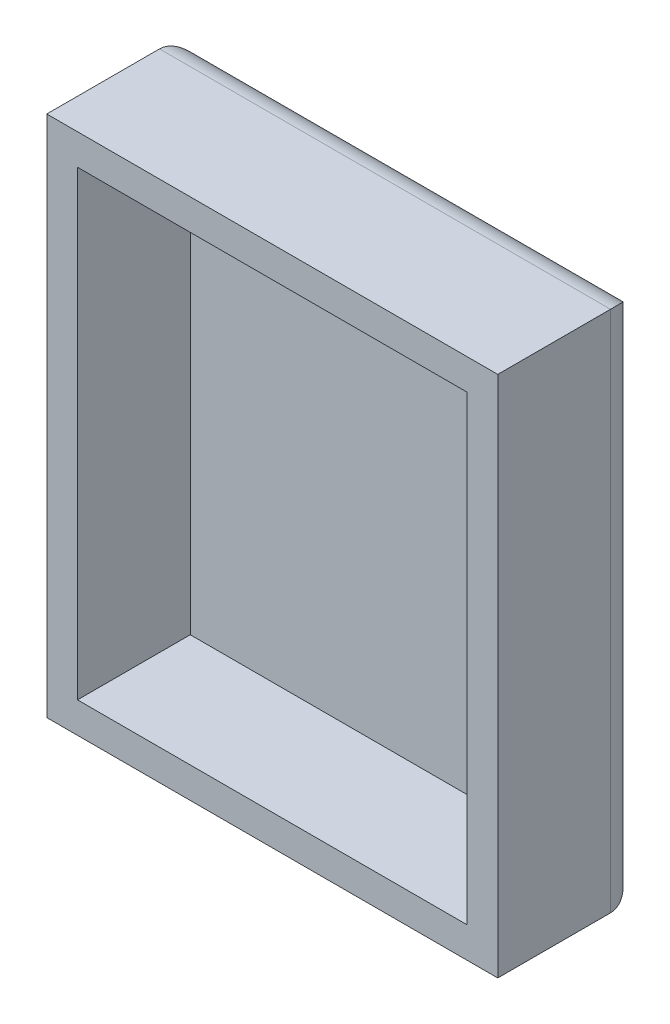
SolidWorks part; units mm, degrees
ref_plane "前基準面" through (0, 0, 0) normal (0, 0, 1) x (1, 0, 0)
ref_plane "上基準面" through (0, 0, 0) normal (0, 1, 0) x (1, 0, 0)
ref_plane "右基準面" through (0, 0, 0) normal (1, 0, 0) x (0, 0, -1)
sketch "草圖1" plane through (0, 0, 0) normal (0, 0, 1) x (1, 0, 0)
  line L1 (-59.7769, 24.8878) -> (-15.7769, 24.8878)
  line L2 (-59.7769, 24.8878) -> (-59.7769, -26.1122)
  line L3 (-59.7769, -26.1122) -> (-15.7769, -26.1122)
  line L4 (-15.7769, 24.8878) -> (-15.7769, -26.1122)
  dimension "D1" = 44
  dimension "D2" = 51
extrude "填料-伸長2" add sketch "草圖1" along normal blind 14
sketch "草圖2" plane through (0, 0, 14) normal (0, 0, 1) x (1, 0, 0)
  line L0 (-15.7769, 24.8878) -> (-59.7769, 24.8878) construction
  line L1 (-56.7769, 21.8878) -> (-18.7769, 21.8878)
  line L2 (-56.7769, 21.8878) -> (-56.7769, -23.1122)
  line L3 (-56.7769, -23.1122) -> (-18.7769, -23.1122)
  line L4 (-18.7769, 21.8878) -> (-18.7769, -23.1122)
  line L5 (-59.7769, 24.8878) -> (-59.7769, -26.1122) construction
  line L6 (-59.7769, -26.1122) -> (-15.7769, -26.1122) construction
  line L7 (-15.7769, -26.1122) -> (-15.7769, 24.8878) construction
  dimension "D1" = 3
  dimension "D2" = 3
  dimension "D3" = 3
  dimension "D4" = 3
extrude "除料-伸長1" cut sketch "草圖2" against normal blind 11
fillet "圓角1" radius 3 4 edges at (-37.7769, 24.8878, 0) (-15.7769, -0.6122, 0) (-37.7769, -26.1122, 0) (-59.7769, -0.6122, 0)
